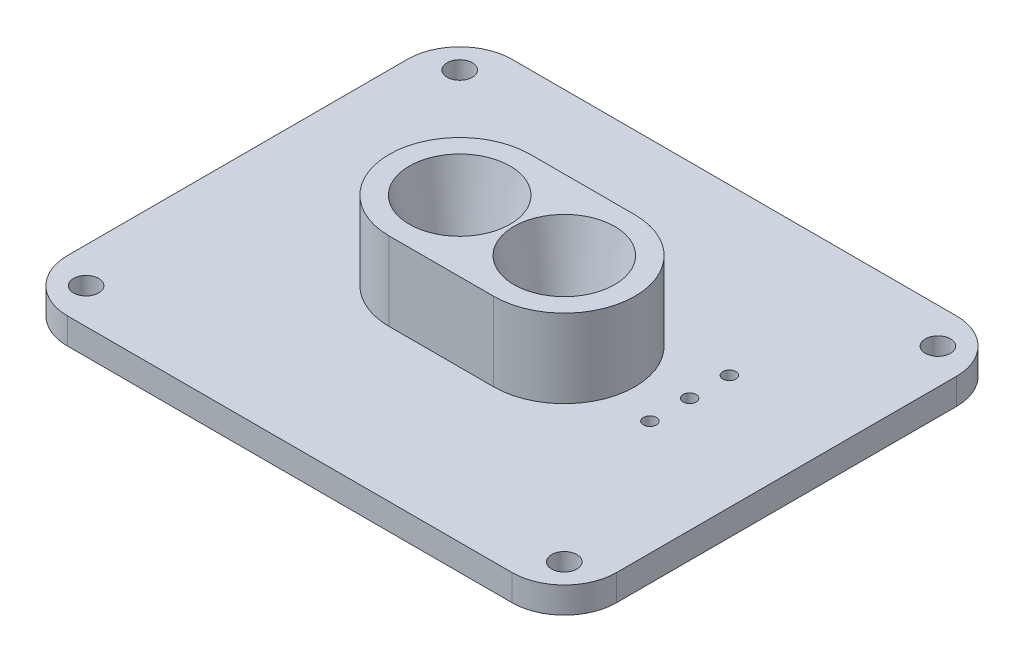
SolidWorks part; units mm, degrees
ref_plane "Front Plane" through (0, 0, 0) normal (0, 0, 1) x (1, 0, 0)
ref_plane "Top Plane" through (0, 0, 0) normal (0, 1, 0) x (1, 0, 0)
ref_plane "Right Plane" through (0, 0, 0) normal (1, 0, 0) x (0, 0, -1)
sketch "Sketch1" plane through (0, 91.488, 0) normal (0, 1, 0) x (1, 0, 0)
  line L4 (-19.6451, -156.9285) -> (88.3049, -156.9285)
  line L5 (97.8299, -147.4035) -> (97.8299, -64.8535)
  line L6 (88.3049, -55.3285) -> (-19.6451, -55.3285)
  line L7 (-29.1701, -64.8535) -> (-29.1701, -147.4035)
  line L8 (-19.6451, -156.9285) -> (88.3049, -156.9285)
  line L9 (97.8299, -147.4035) -> (97.8299, -64.8535)
  line L10 (88.3049, -55.3285) -> (-19.6451, -55.3285)
  line L11 (-29.1701, -64.8535) -> (-29.1701, -147.4035)
  circle A0 centre (-23.7409, -151.4993) radius 2.5527 construction
  circle A1 centre (-23.7409, -151.4993) radius 2.5527 construction
  circle A2 centre (-23.7409, -60.7578) radius 2.5527 construction
  circle A3 centre (-23.7409, -60.7578) radius 2.5527 construction
  arc A4 (-29.1701, -147.4035) -> (-19.6451, -156.9285) centre (-19.6451, -147.4035) ccw
  arc A5 (88.3049, -156.9285) -> (97.8299, -147.4035) centre (88.3049, -147.4035) ccw
  arc A6 (97.8299, -64.8535) -> (88.3049, -55.3285) centre (88.3049, -64.8535) ccw
  arc A7 (-19.6451, -55.3285) -> (-29.1701, -64.8535) centre (-19.6451, -64.8535) ccw
  arc A8 (-29.1701, -147.4035) -> (-19.6451, -156.9285) centre (-19.6451, -147.4035) ccw
  arc A9 (88.3049, -156.9285) -> (97.8299, -147.4035) centre (88.3049, -147.4035) ccw
  arc A10 (97.8299, -64.8535) -> (88.3049, -55.3285) centre (88.3049, -64.8535) ccw
  arc A11 (-19.6451, -55.3285) -> (-29.1701, -64.8535) centre (-19.6451, -64.8535) ccw
  circle A12 centre (92.4006, -60.7578) radius 2.5527 construction
  circle A13 centre (92.4006, -60.7578) radius 2.5527 construction
  circle A14 centre (92.4006, -151.4993) radius 2.5527 construction
  circle A15 centre (92.4006, -151.4993) radius 2.5527 construction
  circle A16 centre (-23.7409, -151.4993) radius 3.0607
  circle A17 centre (-23.7409, -60.7578) radius 3.0607
  circle A18 centre (92.4006, -60.7578) radius 3.0607
  circle A19 centre (92.4006, -151.4993) radius 3.0607
  dimension "D1" = 0
  dimension "D2" = 0.508
extrude "Boss-Extrude1" add sketch "Sketch1" along normal blind 6.35
sketch "Sketch2" plane through (0, 91.488, 0) normal (0, -1, 0) x (1, 0, 0)
  line L0 (97.8299, 106.1285) -> (-29.1701, 106.1285) construction
  line L1 (97.8299, 147.4035) -> (97.8299, 64.8535) construction
  line L2 (-29.1701, 64.8535) -> (-29.1701, 147.4035) construction
  circle A0 centre (47.0299, 106.1285) radius 8.2004
  circle A1 centre (21.6299, 106.1285) radius 8.2004
  point P13 (34.3299, 106.1285)
  dimension "D3" = 16.4008
  dimension "D1" = 25.4
  dimension "D2" = 12.7
extrude "Cut-Extrude1" cut sketch "Sketch2" against normal through all
sketch "Sketch3" plane through (0, 97.838, 0) normal (0, 1, 0) x (1, 0, 0)
  line L0 (47.0299, -106.1285) -> (21.6299, -106.1285) construction
  line L1 (21.6299, -106.1285) -> (47.0299, -106.1285) construction
  line L2 (21.6299, -88.9835) -> (47.0299, -88.9835)
  line L3 (21.6299, -123.2735) -> (47.0299, -123.2735)
  arc A5 (21.6299, -88.9835) -> (21.6299, -123.2735) centre (21.6299, -106.1285) ccw
  arc A12 (47.0299, -123.2735) -> (47.0299, -88.9835) centre (47.0299, -106.1285) ccw
  point P3 (34.3299, -106.1285)
  dimension "D1" = 17.145
extrude "Boss-Extrude2" add sketch "Sketch3" along normal blind 19.05
sketch "Sketch4" plane through (0, 97.838, 0) normal (0, -1, 0) x (1, 0, 0)
  circle A0 centre (21.6299, 106.1285) radius 8.2004 construction
  circle A1 centre (47.0299, 106.1285) radius 8.2004 construction
  circle A2 centre (21.6299, 106.1285) radius 8.2004
  circle A3 centre (47.0299, 106.1285) radius 8.2004
extrude "Cut-Extrude2" cut sketch "Sketch4" against normal blind 19.05 draft 12 draft outward yes
sketch "Sketch5" plane through (0, 97.838, 0) normal (0, 1, 0) x (1, 0, 0)
  line L0 (84.3361, -136.926) -> (84.3361, -86.126) construction
  line L1 (84.3361, -136.926) -> (84.3361, -86.126)
  line L2 (84.3361, -127.274) -> (84.3361, -76.474)
  line L3 (84.3361, -117.622) -> (84.3361, -66.822)
  circle A0 centre (73.2236, -111.526) radius 1.5875
  circle A1 centre (73.2236, -101.874) radius 1.5875
  circle A2 centre (73.2236, -92.222) radius 1.5875
  point P5 (84.3361, -111.526)
  dimension "D1" = 3.175
  dimension "D3" = 11.1125
  dimension "D2" = 3
extrude "Cut-Extrude3" cut sketch "Sketch5" against normal through all contours A0 | A1 | A2
sketch "Sketch6" plane through (0, 97.838, 0) normal (0, 1, 0) x (1, 0, 0)
  line L0 (-32.3451, -64.8535) -> (-32.3451, -147.4035)
  line L1 (-19.6451, -160.1035) -> (88.3049, -160.1035)
  line L2 (101.0049, -147.4035) -> (101.0049, -64.8535)
  line L3 (88.3049, -52.1535) -> (-19.6451, -52.1535)
  line L4 (-19.6451, -156.9285) -> (88.3049, -156.9285)
  line L5 (97.8299, -147.4035) -> (97.8299, -64.8535)
  line L6 (88.3049, -55.3285) -> (-19.6451, -55.3285)
  line L7 (-29.1701, -64.8535) -> (-29.1701, -147.4035)
  line L8 (-19.6451, -156.9285) -> (88.3049, -156.9285)
  line L9 (97.8299, -147.4035) -> (97.8299, -64.8535)
  line L10 (88.3049, -55.3285) -> (-19.6451, -55.3285)
  line L11 (-29.1701, -64.8535) -> (-29.1701, -147.4035)
  arc A0 (-32.3451, -147.4035) -> (-19.6451, -160.1035) centre (-19.6451, -147.4035) ccw
  arc A1 (88.3049, -160.1035) -> (101.0049, -147.4035) centre (88.3049, -147.4035) ccw
  arc A2 (101.0049, -64.8535) -> (88.3049, -52.1535) centre (88.3049, -64.8535) ccw
  arc A3 (-19.6451, -52.1535) -> (-32.3451, -64.8535) centre (-19.6451, -64.8535) ccw
  arc A4 (-29.1701, -147.4035) -> (-19.6451, -156.9285) centre (-19.6451, -147.4035) ccw
  arc A5 (88.3049, -156.9285) -> (97.8299, -147.4035) centre (88.3049, -147.4035) ccw
  arc A6 (97.8299, -64.8535) -> (88.3049, -55.3285) centre (88.3049, -64.8535) ccw
  arc A7 (-19.6451, -55.3285) -> (-29.1701, -64.8535) centre (-19.6451, -64.8535) ccw
  arc A8 (-29.1701, -147.4035) -> (-19.6451, -156.9285) centre (-19.6451, -147.4035) ccw
  arc A9 (88.3049, -156.9285) -> (97.8299, -147.4035) centre (88.3049, -147.4035) ccw
  arc A10 (97.8299, -64.8535) -> (88.3049, -55.3285) centre (88.3049, -64.8535) ccw
  arc A11 (-19.6451, -55.3285) -> (-29.1701, -64.8535) centre (-19.6451, -64.8535) ccw
  dimension "D1" = 0
  dimension "D2" = 3.175
extrude "Boss-Extrude3" add sketch "Sketch6" against normal blind 6.35
